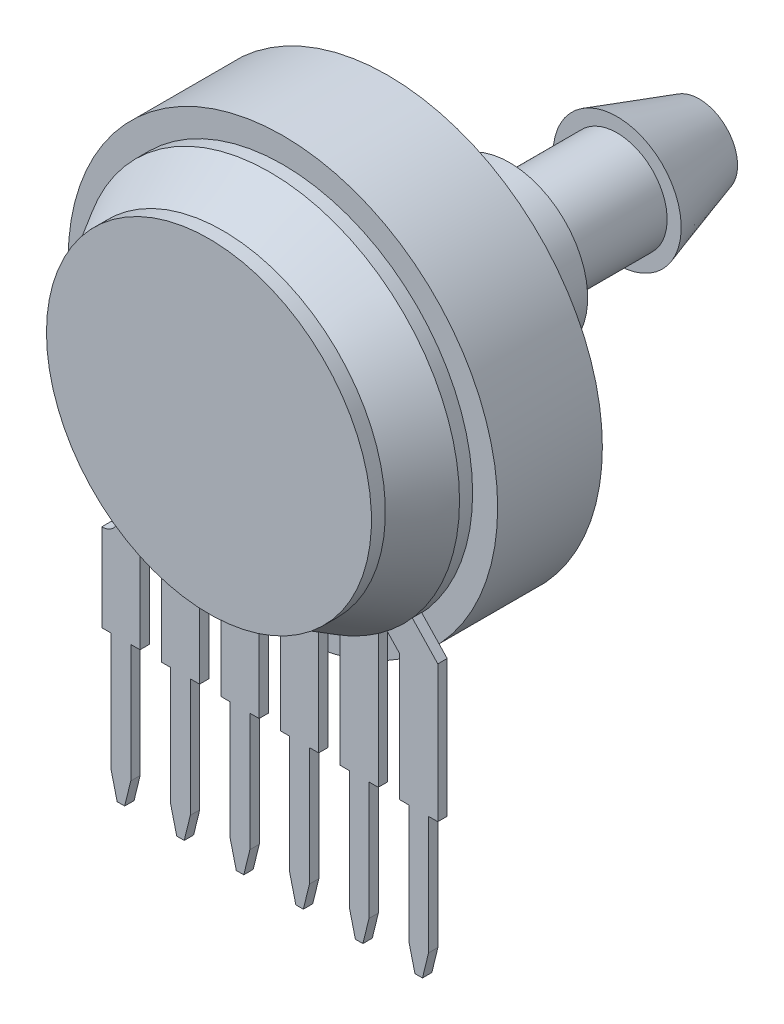
SolidWorks part; units mm, degrees
ref_plane "Front Plane" through (0, 0, 0) normal (0, 0, 1) x (1, 0, 0)
ref_plane "Top Plane" through (0, 0, 0) normal (0, 1, 0) x (1, 0, 0)
ref_plane "Right Plane" through (0, 0, 0) normal (1, 0, 0) x (0, 0, -1)
sketch "Sketch1" plane through (0, 0, 0) normal (0, 0, 1) x (1, 0, 0)
  line L0 (-7.165, -6.4913) -> (-7.165, -7.1728)
  line L1 (-4.625, -8.5934) -> (-4.625, -12.32)
  line L2 (-2.995, -12.32) -> (-2.995, -8.5831)
  line L3 (-7.165, -8.5934) -> (-7.165, -12.32)
  line L4 (-7.165, -12.32) -> (-6.77, -12.32)
  line L5 (-6.77, -12.32) -> (-6.77, -17.3607)
  line L6 (-6.77, -17.3607) -> (-6.5103, -18.42)
  line L7 (-6.5103, -18.42) -> (-6.1897, -18.42)
  line L8 (-6.1897, -18.42) -> (-5.93, -17.3607)
  line L9 (-5.93, -17.3607) -> (-5.93, -12.32)
  line L10 (-5.93, -12.32) -> (-5.535, -12.32)
  line L11 (-5.535, -12.32) -> (-5.535, -8.5831)
  line L12 (-3.39, -12.32) -> (-2.995, -12.32)
  line L13 (-3.39, -17.3607) -> (-3.39, -12.32)
  line L14 (-4.23, -12.32) -> (-4.23, -17.3607)
  line L15 (-4.625, -12.32) -> (-4.23, -12.32)
  line L16 (-3.6497, -18.42) -> (-3.39, -17.3607)
  line L17 (-4.23, -17.3607) -> (-3.9703, -18.42)
  line L18 (-3.9703, -18.42) -> (-3.6497, -18.42)
  line L19 (-2.085, -8.5934) -> (-2.085, -12.32)
  line L20 (-0.455, -12.32) -> (-0.455, -8.5831)
  line L21 (-0.85, -12.32) -> (-0.455, -12.32)
  line L22 (-0.85, -17.3607) -> (-0.85, -12.32)
  line L23 (-1.69, -12.32) -> (-1.69, -17.3607)
  line L24 (-2.085, -12.32) -> (-1.69, -12.32)
  line L25 (-1.1097, -18.42) -> (-0.85, -17.3607)
  line L26 (-1.69, -17.3607) -> (-1.4303, -18.42)
  line L27 (-1.4303, -18.42) -> (-1.1097, -18.42)
  line L28 (0.455, -8.5934) -> (0.455, -12.32)
  line L29 (2.085, -12.32) -> (2.085, -8.5831)
  line L30 (1.69, -12.32) -> (2.085, -12.32)
  line L31 (1.69, -17.3607) -> (1.69, -12.32)
  line L32 (0.85, -12.32) -> (0.85, -17.3607)
  line L33 (0.455, -12.32) -> (0.85, -12.32)
  line L34 (1.4303, -18.42) -> (1.69, -17.3607)
  line L35 (0.85, -17.3607) -> (1.1097, -18.42)
  line L36 (1.1097, -18.42) -> (1.4303, -18.42)
  line L37 (2.995, -8.5934) -> (2.995, -12.32)
  line L38 (4.625, -12.32) -> (4.625, -8.5831)
  line L39 (4.23, -12.32) -> (4.625, -12.32)
  line L40 (4.23, -17.3607) -> (4.23, -12.32)
  line L41 (3.39, -12.32) -> (3.39, -17.3607)
  line L42 (2.995, -12.32) -> (3.39, -12.32)
  line L43 (3.9703, -18.42) -> (4.23, -17.3607)
  line L44 (3.39, -17.3607) -> (3.6497, -18.42)
  line L45 (3.6497, -18.42) -> (3.9703, -18.42)
  line L46 (5.535, -8.5934) -> (5.535, -12.32)
  line L47 (7.165, -12.32) -> (7.165, -8.5831)
  line L48 (6.77, -12.32) -> (7.165, -12.32)
  line L49 (6.77, -17.3607) -> (6.77, -12.32)
  line L50 (5.93, -12.32) -> (5.93, -17.3607)
  line L51 (5.535, -12.32) -> (5.93, -12.32)
  line L52 (6.5103, -18.42) -> (6.77, -17.3607)
  line L53 (5.93, -17.3607) -> (6.1897, -18.42)
  line L54 (6.1897, -18.42) -> (6.5103, -18.42)
  line L55 (-7.165, -8.5934) -> (-4.625, -8.5934) construction
  line L56 (-6.35, -18.42) -> (-6.35, -17.3607) construction
  line L57 (-6.35, -17.3607) -> (-6.77, -17.3607) construction
  line L58 (-5.93, -17.3607) -> (-6.35, -17.3607) construction
  line L59 (0.455, -12.32) -> (0, -12.32) construction
  line L60 (0, -12.32) -> (-0.455, -12.32) construction
  line L62 (0, 0) -> (-11.555, 0) construction
  line L64 (0, 0) -> (0, 0.5736) construction
  line L67 (-7.165, -6.4913) -> (-5.0517, -4.2591)
  line L68 (-5.535, -8.5831) -> (-5.535, -6.9232)
  line L69 (-5.535, -6.9232) -> (-3.8372, -5.1299)
  line L70 (-7.165, -6.4913) -> (-5.535, -6.9232) construction
  line L71 (-6.35, -6.7073) -> (0, 0) construction
  line L72 (0, 0) -> (0, -8.5831) construction
  line L73 (5.535, -6.9232) -> (3.8372, -5.1299)
  line L74 (5.535, -8.5831) -> (5.535, -6.9232)
  line L75 (7.165, -6.4913) -> (5.0517, -4.2591)
  arc A0 (-7.165, -7.1728) -> (-7.165, -8.5934) centre (-7.165, -7.8831) cw
  circle A1 centre (0, 0) radius 0.8115
  circle A2 centre (0, 0) radius 5.401
  circle A7 centre (0, 0) radius 6.8776
  circle A8 centre (0, 0) radius 7.9339
  dimension "D1" = 2.54
  dimension "D2" = 1.63
  dimension "D3" = 0.84
  dimension "D4" = 6.1
  dimension "D5" = 18.42
sketch "Sketch2" plane through (0, 0, 0) normal (1, 0, 0) x (0, 0, -1)
  line L18 (0, 7.9084) -> (0, -17.9671)
  line L19 (-0.2, -8.0916) -> (-2.2009, -6.93)
  line L21 (-2.2009, -6.93) -> (-2.795, -6.93)
  line L26 (-2.795, 6.93) -> (-2.0963, 6.93)
  line L27 (-0.3582, 7.9084) -> (0, 7.9084)
  line L28 (-2.0963, 6.93) -> (-0.3582, 7.9084)
  line L48 (0, 0) -> (1.7159, 0) construction
  line L49 (0, 7.9084) -> (0, 9.9029) construction
  line L50 (4.8238, 6.5038) -> (5.2679, 6.5038)
  line L51 (5.2679, 6.5038) -> (5.2679, 3.3343)
  line L52 (5.2679, 3.3343) -> (10.0223, 3.3343)
  line L53 (10.0223, 3.3343) -> (10.0223, 2.1321)
  line L54 (10.0223, 2.1321) -> (14.6126, 2.1321)
  line L55 (14.6126, 2.1321) -> (14.6126, 2.7332)
  line L56 (14.6126, 2.7332) -> (18.1101, 1.6402)
  line L57 (4.8238, 9.1593) -> (4.8238, 6.5038)
  line L58 (0.3582, 9.1593) -> (4.8238, 9.1593)
  line L59 (0.3582, 7.9084) -> (0.3582, 9.1593)
  line L60 (18.1101, 0) -> (4.175, 0)
  line L61 (18.1101, -1.6402) -> (18.1101, 0)
  line L62 (14.6126, -2.7332) -> (18.1101, -1.6402)
  line L63 (14.6126, -2.1321) -> (14.6126, -2.7332)
  line L64 (10.0223, -2.1321) -> (14.6126, -2.1321)
  line L65 (10.0223, -3.3343) -> (10.0223, -2.1321)
  line L66 (5.2679, -3.3343) -> (10.0223, -3.3343)
  line L67 (5.2679, -6.5038) -> (5.2679, -3.3343)
  line L68 (4.8238, -6.5038) -> (5.2679, -6.5038)
  line L69 (4.8238, -9.1593) -> (4.8238, -6.5038)
  line L70 (-0.2, -17.9671) -> (-0.2, -8.0916)
  line L71 (0.3582, -9.1593) -> (4.8238, -9.1593)
  line L72 (-2.795, -6.93) -> (-2.795, 6.93)
  line L76 (2.795, -6.93) -> (2.795, 6.93)
  line L79 (0.2, -17.9671) -> (0.2, -8.0916)
  line L80 (0, -17.9671) -> (0.2, -17.9671)
sketch "Sketch7" plane through (0, 0, 0) normal (0, 0, 1) x (1, 0, 0)
  line L1 (-5.93, -12.32) -> (-5.535, -12.32) construction
  line L2 (-5.93, -17.3607) -> (-5.93, -12.32) construction
  line L3 (-6.1897, -18.42) -> (-5.93, -17.3607) construction
  line L4 (-6.5103, -18.42) -> (-6.1897, -18.42) construction
  line L5 (-6.77, -17.3607) -> (-6.5103, -18.42) construction
  line L6 (-6.77, -12.32) -> (-6.77, -17.3607) construction
  line L7 (-7.165, -12.32) -> (-6.77, -12.32) construction
  line L8 (-7.165, -8.5934) -> (-7.165, -12.32) construction
  line L10 (-4.625, -8.5934) -> (-4.625, -12.32) construction
  line L11 (-4.625, -12.32) -> (-4.23, -12.32) construction
  line L12 (-4.23, -12.32) -> (-4.23, -17.3607) construction
  line L13 (-4.23, -17.3607) -> (-3.9703, -18.42) construction
  line L14 (-3.9703, -18.42) -> (-3.6497, -18.42) construction
  line L15 (-3.6497, -18.42) -> (-3.39, -17.3607) construction
  line L16 (-3.39, -17.3607) -> (-3.39, -12.32) construction
  line L17 (-3.39, -12.32) -> (-2.995, -12.32) construction
  line L18 (-2.995, -12.32) -> (-2.995, -8.5831) construction
  line L19 (-0.455, -12.32) -> (-0.455, -8.5831) construction
  line L20 (-0.85, -12.32) -> (-0.455, -12.32) construction
  line L21 (-0.85, -17.3607) -> (-0.85, -12.32) construction
  line L22 (-1.1097, -18.42) -> (-0.85, -17.3607) construction
  line L23 (-1.4303, -18.42) -> (-1.1097, -18.42) construction
  line L24 (-1.69, -17.3607) -> (-1.4303, -18.42) construction
  line L25 (-1.69, -12.32) -> (-1.69, -17.3607) construction
  line L26 (-2.085, -12.32) -> (-1.69, -12.32) construction
  line L27 (-2.085, -8.5934) -> (-2.085, -12.32) construction
  line L28 (4.625, -12.32) -> (4.625, -8.5831) construction
  line L29 (4.23, -12.32) -> (4.625, -12.32) construction
  line L30 (4.23, -17.3607) -> (4.23, -12.32) construction
  line L31 (3.9703, -18.42) -> (4.23, -17.3607) construction
  line L32 (3.6497, -18.42) -> (3.9703, -18.42) construction
  line L33 (3.39, -17.3607) -> (3.6497, -18.42) construction
  line L34 (3.39, -12.32) -> (3.39, -17.3607) construction
  line L35 (2.995, -12.32) -> (3.39, -12.32) construction
  line L36 (2.995, -8.5934) -> (2.995, -12.32) construction
  line L37 (0.455, -8.5934) -> (0.455, -12.32) construction
  line L38 (0.455, -12.32) -> (0.85, -12.32) construction
  line L39 (0.85, -12.32) -> (0.85, -17.3607) construction
  line L40 (0.85, -17.3607) -> (1.1097, -18.42) construction
  line L41 (1.1097, -18.42) -> (1.4303, -18.42) construction
  line L42 (1.4303, -18.42) -> (1.69, -17.3607) construction
  line L43 (1.69, -17.3607) -> (1.69, -12.32) construction
  line L44 (1.69, -12.32) -> (2.085, -12.32) construction
  line L45 (2.085, -12.32) -> (2.085, -8.5831) construction
  line L47 (5.535, -12.32) -> (5.93, -12.32) construction
  line L48 (5.93, -12.32) -> (5.93, -17.3607) construction
  line L49 (5.93, -17.3607) -> (6.1897, -18.42) construction
  line L50 (6.1897, -18.42) -> (6.5103, -18.42) construction
  line L51 (6.5103, -18.42) -> (6.77, -17.3607) construction
  line L52 (6.77, -17.3607) -> (6.77, -12.32) construction
  line L53 (6.77, -12.32) -> (7.165, -12.32) construction
  line L55 (-7.165, -6.4913) -> (-7.165, -7.1728) construction
  line L56 (-5.93, -12.32) -> (-5.535, -12.32)
  line L57 (-5.93, -17.3607) -> (-5.93, -12.32)
  line L58 (-6.1897, -18.42) -> (-5.93, -17.3607)
  line L59 (-6.5103, -18.42) -> (-6.1897, -18.42)
  line L60 (-6.77, -17.3607) -> (-6.5103, -18.42)
  line L61 (-6.77, -12.32) -> (-6.77, -17.3607)
  line L62 (-7.165, -12.32) -> (-6.77, -12.32)
  line L63 (-7.165, -8.5934) -> (-7.165, -12.32)
  line L64 (-7.165, -6.4913) -> (-5.0517, -4.2591) construction
  line L65 (-4.625, -6.4464) -> (-4.625, -12.32)
  line L66 (-4.625, -12.32) -> (-4.23, -12.32)
  line L67 (-4.23, -12.32) -> (-4.23, -17.3607)
  line L68 (-4.23, -17.3607) -> (-3.9703, -18.42)
  line L69 (-3.9703, -18.42) -> (-3.6497, -18.42)
  line L70 (-3.6497, -18.42) -> (-3.39, -17.3607)
  line L71 (-3.39, -17.3607) -> (-3.39, -12.32)
  line L72 (-3.39, -12.32) -> (-2.995, -12.32)
  line L73 (-2.995, -12.32) -> (-2.995, -7.3469)
  line L74 (-0.455, -12.32) -> (-0.455, -7.9208)
  line L75 (-0.85, -12.32) -> (-0.455, -12.32)
  line L76 (-0.85, -17.3607) -> (-0.85, -12.32)
  line L77 (-1.1097, -18.42) -> (-0.85, -17.3607)
  line L78 (-1.4303, -18.42) -> (-1.1097, -18.42)
  line L79 (-1.69, -17.3607) -> (-1.4303, -18.42)
  line L80 (-1.69, -12.32) -> (-1.69, -17.3607)
  line L81 (-2.085, -12.32) -> (-1.69, -12.32)
  line L82 (-2.085, -7.655) -> (-2.085, -12.32)
  line L83 (4.625, -12.32) -> (4.625, -6.4464)
  line L84 (4.23, -12.32) -> (4.625, -12.32)
  line L85 (4.23, -17.3607) -> (4.23, -12.32)
  line L86 (3.9703, -18.42) -> (4.23, -17.3607)
  line L87 (3.6497, -18.42) -> (3.9703, -18.42)
  line L88 (3.39, -17.3607) -> (3.6497, -18.42)
  line L89 (3.39, -12.32) -> (3.39, -17.3607)
  line L90 (2.995, -12.32) -> (3.39, -12.32)
  line L91 (2.995, -7.3469) -> (2.995, -12.32)
  line L92 (0.455, -7.9208) -> (0.455, -12.32)
  line L93 (0.455, -12.32) -> (0.85, -12.32)
  line L94 (0.85, -12.32) -> (0.85, -17.3607)
  line L95 (0.85, -17.3607) -> (1.1097, -18.42)
  line L96 (1.1097, -18.42) -> (1.4303, -18.42)
  line L97 (1.4303, -18.42) -> (1.69, -17.3607)
  line L98 (1.69, -17.3607) -> (1.69, -12.32)
  line L99 (1.69, -12.32) -> (2.085, -12.32)
  line L100 (2.085, -12.32) -> (2.085, -7.655)
  line L101 (-5.535, -8.5831) -> (-5.535, -6.9232) construction
  line L102 (5.535, -12.32) -> (5.93, -12.32)
  line L103 (5.93, -12.32) -> (5.93, -17.3607)
  line L104 (5.93, -17.3607) -> (6.1897, -18.42)
  line L105 (6.1897, -18.42) -> (6.5103, -18.42)
  line L106 (6.5103, -18.42) -> (6.77, -17.3607)
  line L107 (6.77, -17.3607) -> (6.77, -12.32)
  line L108 (6.77, -12.32) -> (7.165, -12.32)
  line L109 (-5.535, -6.9232) -> (-3.8372, -5.1299) construction
  line L110 (7.165, -6.4913) -> (5.0517, -4.2591) construction
  line L111 (5.535, -6.9232) -> (3.8372, -5.1299) construction
  line L112 (5.535, -8.5831) -> (5.535, -6.9232) construction
  line L113 (7.165, -12.32) -> (7.165, -8.5831) construction
  line L114 (-7.165, -6.4913) -> (-7.165, -7.1728)
  line L115 (-7.165, -6.4913) -> (-5.9684, -5.2274)
  line L116 (-5.535, -12.32) -> (-5.535, -6.9232)
  line L117 (-5.535, -6.9232) -> (-4.8932, -6.2453)
  line L118 (7.165, -6.4913) -> (5.9684, -5.2274)
  line L119 (5.535, -6.9232) -> (4.8932, -6.2453)
  line L120 (5.535, -12.32) -> (5.535, -6.9232)
  line L121 (7.165, -12.32) -> (7.165, -6.4913)
  arc A0 (-7.165, -8.5934) -> (-7.165, -7.1728) centre (-7.165, -7.8831) ccw construction
  arc A1 (-7.165, -8.5934) -> (-7.165, -7.1728) centre (-7.165, -7.8831) ccw
  circle A2 centre (0, 0) radius 7.9339 construction
  arc A3 (-5.9684, -5.2274) -> (-4.8932, -6.2453) centre (0, 0) ccw
  arc A4 (-2.085, -7.655) -> (-0.455, -7.9208) centre (0, 0) ccw
  arc A5 (0.455, -7.9208) -> (2.085, -7.655) centre (0, 0) ccw
  arc A6 (2.995, -7.3469) -> (4.625, -6.4464) centre (0, 0) ccw
  arc A7 (4.8932, -6.2453) -> (5.9684, -5.2274) centre (0, 0) ccw
  arc A8 (-4.625, -6.4464) -> (-2.995, -7.3469) centre (0, 0) ccw
extrude "Extrude6" add sketch "Sketch7" along normal up to vertex (0.2 mm away) and the other way up to vertex (0.2 mm away) up to point (0, -17.9671, 0.2) other way up to point (0, -17.9671, -0.2)
sketch "Sketch8" plane through (0, 0, 0) normal (1, 0, 0) x (0, 0, -1)
  line L2 (0, 7.9339) -> (0, -7.9339) construction
  line L4 (0, 7.9339) -> (0, -7.9339) construction
  line L6 (0, 0) -> (-6.1451, 0) construction
  line L19 (18.1101, 0) -> (4.175, 0) construction
  line L20 (18.1101, -1.6402) -> (18.1101, 0) construction
  line L21 (14.6126, -2.7332) -> (18.1101, -1.6402) construction
  line L27 (14.6126, -2.1321) -> (14.6126, -2.7332) construction
  line L28 (10.0223, -2.1321) -> (14.6126, -2.1321) construction
  line L29 (10.0223, -3.3343) -> (10.0223, -2.1321) construction
  line L31 (5.2679, -3.3343) -> (10.0223, -3.3343) construction
  line L32 (5.2679, -6.5038) -> (5.2679, -3.3343) construction
  line L33 (4.8238, -6.5038) -> (5.2679, -6.5038) construction
  line L34 (4.8238, -9.1593) -> (4.8238, -6.5038) construction
  line L35 (0.3582, -9.1593) -> (4.8238, -9.1593) construction
  line L42 (-2.795, -6.93) -> (-2.795, 6.93) construction
  line L43 (-2.2009, -6.93) -> (-2.795, -6.93) construction
  line L44 (-0.2, -8.0916) -> (-2.2009, -6.93) construction
  line L47 (0.3582, -9.1593) -> (0.3582, -8.0916)
  line L48 (0.3582, -8.0916) -> (-0.2, -8.0916)
  line L57 (18.1101, 0) -> (-2.795, 0)
  line L58 (18.1101, -1.6402) -> (18.1101, 0)
  line L59 (14.6126, -2.7332) -> (18.1101, -1.6402)
  line L60 (14.6126, -2.1321) -> (14.6126, -2.7332)
  line L61 (10.0223, -2.1321) -> (14.6126, -2.1321)
  line L62 (10.0223, -3.3343) -> (10.0223, -2.1321)
  line L63 (5.2679, -3.3343) -> (10.0223, -3.3343)
  line L64 (5.2679, -6.5038) -> (5.2679, -3.3343)
  line L65 (4.8238, -6.5038) -> (5.2679, -6.5038)
  line L66 (4.8238, -9.1593) -> (4.8238, -6.5038)
  line L67 (0.3582, -9.1593) -> (4.8238, -9.1593)
  line L74 (-2.795, -6.93) -> (-2.795, 0)
  line L75 (-2.2009, -6.93) -> (-2.795, -6.93)
  line L76 (-0.2, -8.0916) -> (-2.2009, -6.93)
revolve "Revolve1" add sketch "Sketch8" angle 360 about L6
hole_wizard "Ø1.0 (1) Diameter Hole1" positions "3DSketch1" profile "Sketch9" hole size "Ø1.0" standard "Ansi Metric"
sketch3d "3DSketch1"
  circle A1 centre (0, 0, -18.1101) radius 1.6402 construction
  point P0 (0, 0, -18.1101)
  point P12 (0, 0, -19.7503)
sketch "Sketch9" plane through (0, 0, -18.1101) normal (1, 0, 0) x (0, 1, 0)
  line L0 (0, 0) -> (0, 14.2704)
  line L1 (0, 14.2704) -> (0.5, 13.97)
  line L2 (0.5, 13.97) -> (0.5, 0)
  line L5 (0.5, 0) -> (0, 0)
  line L10 (0, 14.2704) -> (-0.5, 13.97) construction
  line L11 (0, -6.35) -> (0, 107.95) construction
  dimension "Hole Dia." = 1
  dimension "Hole Depth" = 13.97
  dimension "Drill Angle" = 118
